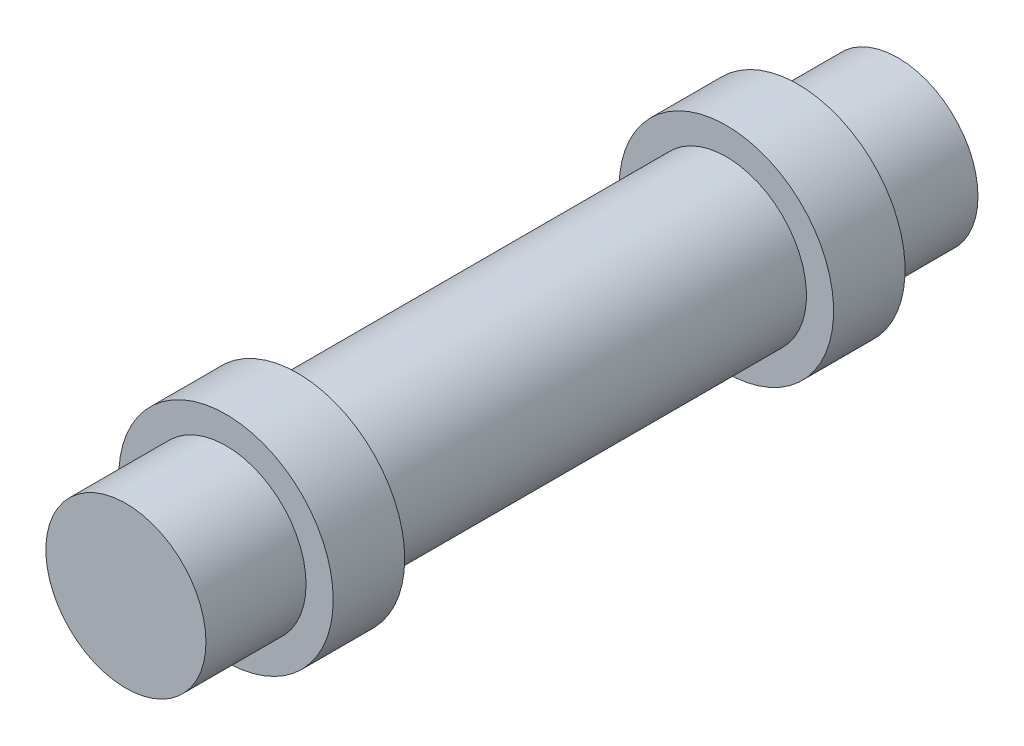
SolidWorks part; units mm, degrees
ref_plane "Alzado" through (0, 0, 0) normal (0, 0, 1) x (1, 0, 0)
ref_plane "Planta" through (0, 0, 0) normal (0, 1, 0) x (1, 0, 0)
ref_plane "Vista lateral" through (0, 0, 0) normal (1, 0, 0) x (0, 0, -1)
sketch "Croquis1" plane through (0, 0, 0) normal (0, 0, 1) x (1, 0, 0)
  circle A0 centre (0, 0) radius 5.6
  dimension "D1" = 11.2
extrude "Saliente-Extruir1" add sketch "Croquis1" along normal blind 54
ref_plane "Plano2" through (0, 0, 47) normal (0, 0, 1) x (1, 0, 0)
sketch "Croquis2" plane through (0, 0, 47) normal (0, 0, 1) x (1, 0, 0)
  circle A0 centre (0, 0) radius 7.5
  dimension "D1" = 15
extrude "Saliente-Extruir2" add sketch "Croquis2" against normal blind 5
ref_plane "Plano3" through (0, 0, 7) normal (0, 0, -1) x (-1, 0, 0)
sketch "Croquis3" plane through (0, 0, 7) normal (0, 0, -1) x (-1, 0, 0)
  circle A0 centre (0, 0) radius 7.5
extrude "Saliente-Extruir3" add sketch "Croquis3" against normal blind 5
